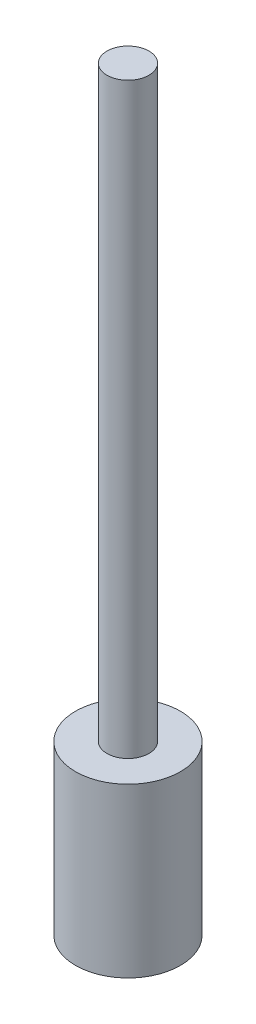
SolidWorks part; units mm, degrees
ref_plane "Front Plane" through (0, 0, 0) normal (0, 0, 1) x (1, 0, 0)
ref_plane "Top Plane" through (0, 0, 0) normal (0, 1, 0) x (1, 0, 0)
ref_plane "Right Plane" through (0, 0, 0) normal (1, 0, 0) x (0, 0, -1)
sketch "Sketch1" plane through (0, 0, 0) normal (0, 1, 0) x (1, 0, 0)
  circle A0 centre (0, 0) radius 12.5
  dimension "D1" = 25
extrude "Boss-Extrude1" add sketch "Sketch1" along normal blind 40
sketch "Sketch2" plane through (0, 40, 0) normal (0, 1, 0) x (1, 0, 0)
  circle A0 centre (0, 0) radius 5
  dimension "D1" = 10
extrude "Boss-Extrude2" add sketch "Sketch2" along normal blind 140
